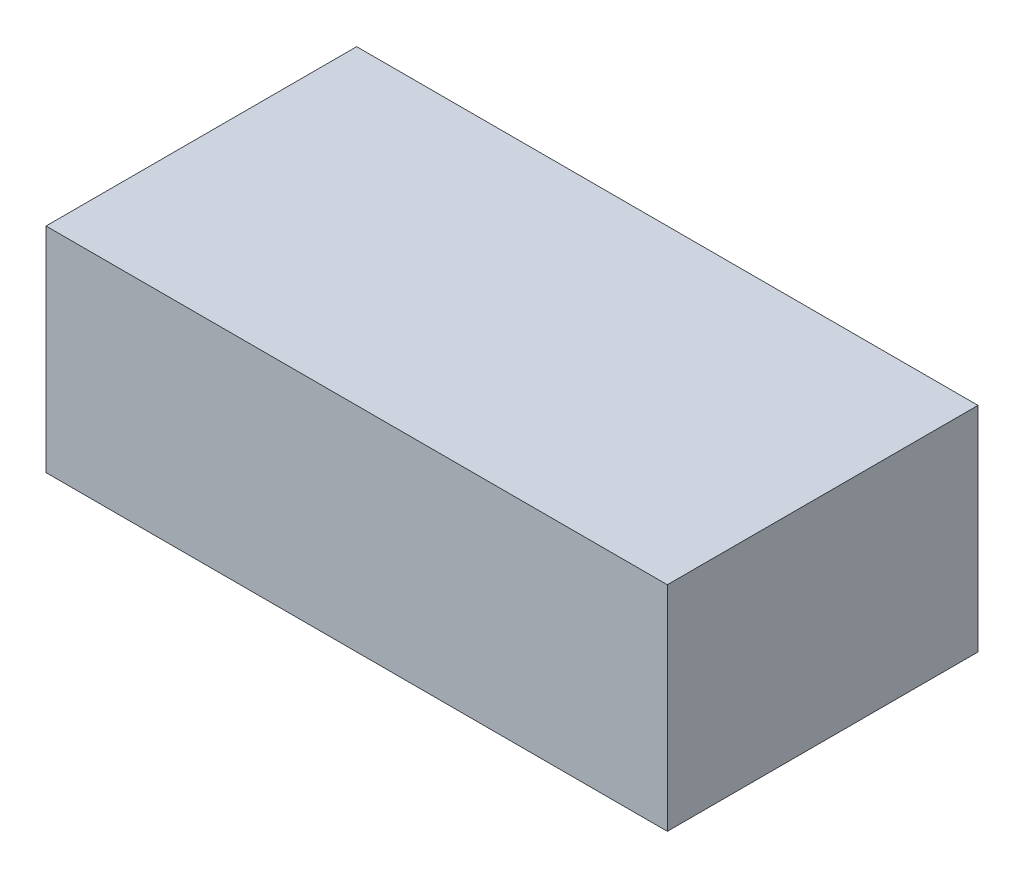
SolidWorks part; units mm, degrees
ref_plane "Front Plane" through (0, 0, 0) normal (0, 0, 1) x (1, 0, 0)
ref_plane "Top Plane" through (0, 0, 0) normal (0, 1, 0) x (1, 0, 0)
ref_plane "Right Plane" through (0, 0, 0) normal (1, 0, 0) x (0, 0, -1)
sketch "Sketch1" plane through (0, 0, 0) normal (0, 1, 0) x (1, 0, 0)
  line L1 (-1.6, -0.8) -> (1.6, -0.8)
  line L2 (-1.6, -0.8) -> (-1.6, 0.8)
  line L3 (-1.6, 0.8) -> (1.6, 0.8)
  line L4 (1.6, -0.8) -> (1.6, 0.8)
  line L5 (-1.6, -0.8) -> (1.6, 0.8) construction
  line L6 (-1.6, 0.8) -> (1.6, -0.8) construction
  point P0 (0, 0)
  dimension "D1" = 3.2
  dimension "D2" = 1.6
extrude "Boss-Extrude1" add sketch "Sketch1" along normal blind 1.1
